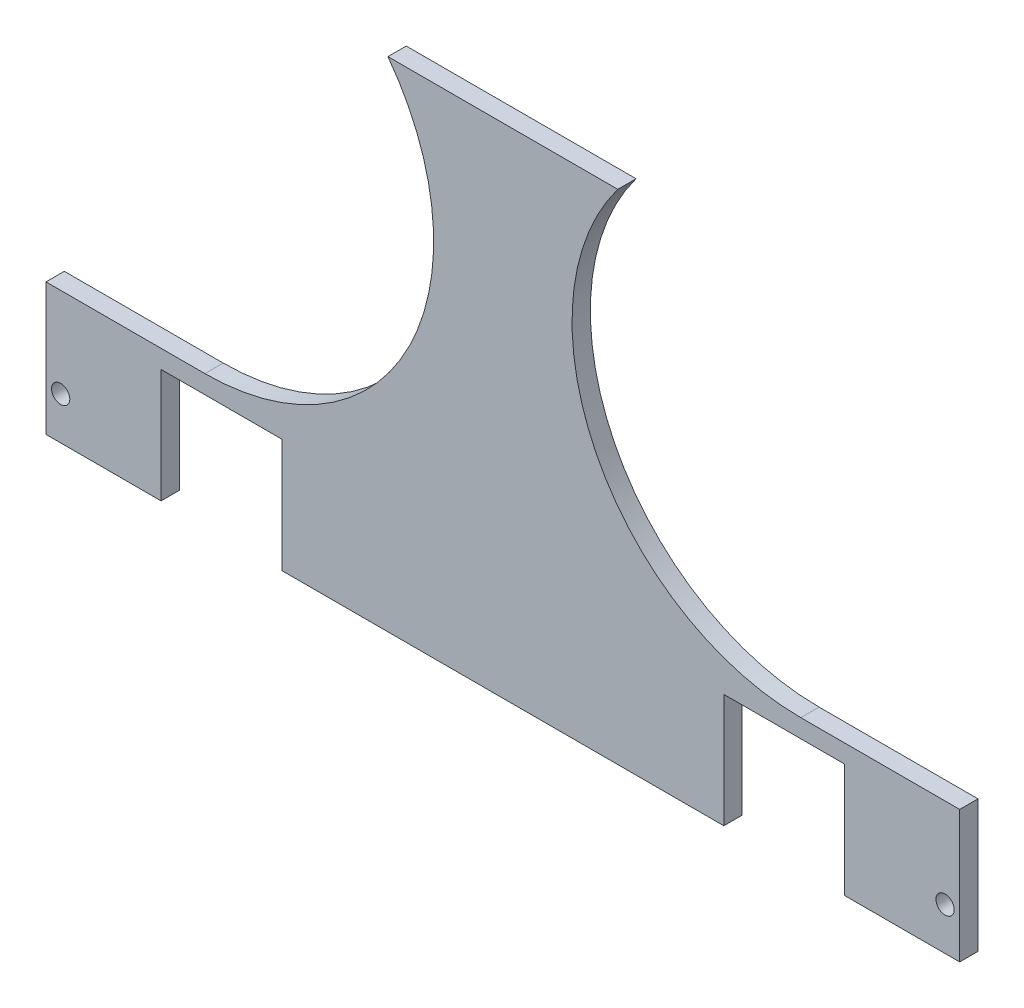
SolidWorks part; units mm, degrees
ref_plane "Front Plane" through (0, 0, 0) normal (0, 0, 1) x (1, 0, 0)
ref_plane "Top Plane" through (0, 0, 0) normal (0, 1, 0) x (1, 0, 0)
ref_plane "Right Plane" through (0, 0, 0) normal (1, 0, 0) x (0, 0, -1)
sketch "Sketch1" plane through (0, 0, 0) normal (0, 0, 1) x (1, 0, 0)
  line L0 (124.8, -69) -> (124.8, -336.4) construction
  line L1 (0, -69) -> (249.6, -69)
  line L2 (0, -69) -> (0, -336.4)
  line L3 (0, -336.4) -> (249.6, -336.4)
  line L4 (249.6, -69) -> (249.6, -336.4)
  line L9 (185.16, -174) -> (218.16, -174)
  line L10 (185.16, -174) -> (185.16, -264)
  line L11 (185.16, -264) -> (218.16, -264)
  line L12 (218.16, -174) -> (218.16, -264)
  line L13 (156.1971, -69) -> (93.4029, -69) construction
  line L14 (31.44, -219) -> (218.16, -219) construction
  line L15 (249.6, -336.4) -> (249.6, -169) construction
  line L21 (0, -169) -> (0, -336.4) construction
  line L25 (249.6, -336.4) -> (0, -336.4) construction
  line L52 (204.16, -174) -> (204.16, -264) construction
  line L53 (194.16, -174) -> (214.16, -174) construction
  line L54 (194.16, -174) -> (194.16, -264) construction
  line L55 (194.16, -264) -> (214.16, -264) construction
  line L56 (214.16, -174) -> (214.16, -264) construction
  line L102 (245.6, -193.5) -> (245.6, -244.5) construction
  line L103 (218.16, -219) -> (245.6, -219) construction
  line L134 (31.44, -219) -> (4, -219) construction
  line L135 (4, -193.5) -> (4, -244.5) construction
  line L139 (35.44, -174) -> (35.44, -264) construction
  line L140 (55.44, -264) -> (35.44, -264) construction
  line L141 (55.44, -174) -> (55.44, -264) construction
  line L142 (55.44, -174) -> (35.44, -174) construction
  line L143 (45.44, -174) -> (45.44, -264) construction
  line L154 (31.44, -174) -> (31.44, -264)
  line L155 (64.44, -264) -> (31.44, -264)
  line L156 (64.44, -174) -> (64.44, -264)
  line L157 (64.44, -174) -> (31.44, -174)
  circle A84 centre (245.6, -193.5) radius 2.5
  circle A85 centre (245.6, -244.5) radius 2.5
  circle A236 centre (4, -244.5) radius 2.5
  circle A237 centre (4, -193.5) radius 2.5
  dimension "D5" = 20
  dimension "D15" = 5
  dimension "D16" = 5
  dimension "D2" = 105
  dimension "D3" = 4
  dimension "D4" = 90
  dimension "D6" = 90
  dimension "D7" = 9
  dimension "D14" = 89.36
  dimension "D17" = 25.5
  dimension "D18" = 4
extrude "Boss-Extrude1" add sketch "Sketch1" along normal blind 5
sketch "Sketch2" plane through (0, 0, 5) normal (0, 0, 1) x (1, 0, 0)
  line L0 (-0.8818, -199.1061) -> (0.8939, -68.1182) construction
  line L1 (377.0835, -204.2298) -> (378.8591, -73.2419) construction
  line L2 (-0.8818, -199.1061) -> (377.0835, -204.2298) construction
  line L3 (14.5032, -15.3834) -> (11.5694, -19.4322) construction
  line L4 (11.5694, -19.4322) -> (65.6935, -58.6513) construction
  line L5 (75.64, -59.684) -> (14.5032, -15.3834) construction
  line L6 (0.8939, -68.1182) -> (378.8591, -73.2419) construction
  line L7 (0.8532, -71.1179) -> (378.8185, -76.2416) construction
  line L8 (-0.8412, -196.1064) -> (377.1241, -201.2301) construction
  line L9 (14.5032, -15.3834) -> (17.4371, -11.3347) construction
  line L10 (17.4371, -11.3347) -> (71.5611, -50.5537) construction
  line L11 (252.1356, -199.5358) -> (253.8299, -74.5473) construction
  line L12 (127.9943, -135.3472) -> (252.9828, -137.0415) construction
  line L13 (127.1471, -197.8414) -> (128.8414, -72.8529) construction
  line L14 (249.6, -69) -> (0, -69) construction
  line L15 (0, -69) -> (0, -336.4) construction
  circle A0 centre (65.5, -134.5) radius 62.5 construction
  circle A1 centre (315.477, -137.8887) radius 62.5 construction
  circle A2 centre (65.5, -134.5) radius 65.5 construction
  circle A3 centre (190.4885, -136.1943) radius 62.5 construction
  circle A4 centre (75.64, -59.684) radius 75.5 construction
  circle A5 centre (75.64, -59.684) radius 2.5 construction
  circle A6 centre (55.3961, -45.015) radius 1.5 construction
  arc A7 (65.6935, -58.6513) -> (71.5611, -50.5537) centre (75.64, -59.684) ccw construction
  dimension "D1" = 125
  dimension "D2" = 125
  dimension "D3" = 5
  dimension "D6" = 3
  dimension "D7" = 10
  dimension "D10" = 125
  dimension "D8" = 3
  dimension "D4" = 5
  dimension "D5" = 25
  dimension "D9" = 5
ref_plane "Plane1"
sketch "Sketch6" plane through (0, 0, 5) normal (0, 0, 1) x (1, 0, 0)
  line L9 (43.4029, -44) -> (0, -44)
  line L10 (206.1971, -169) -> (249.6, -169)
  line L11 (249.6, -169) -> (249.6, -44)
  line L12 (249.6, -44) -> (206.1971, -44)
  line L13 (43.4029, -44) -> (0, -44) construction
  line L18 (43.4029, -169) -> (0, -169)
  line L19 (43.4029, -169) -> (0, -169) construction
  line L23 (0, -44) -> (0, -169)
  line L24 (0, -336.4) -> (249.6, -336.4)
  line L25 (0, -44) -> (0, -169) construction
  line L26 (0, -336.4) -> (0, -205.0954)
  line L27 (249.6, -336.4) -> (249.6, -205.0954)
  line L28 (0, -205.0954) -> (249.6, -205.0954)
  line L29 (249.6, -44) -> (249.6, -169) construction
  line L31 (64.8, -205.0954) -> (59.8, -205.0954) construction
  arc A1 (206.1971, -44) -> (206.1971, -169) centre (206.1971, -106.5) ccw construction
  arc A2 (206.1971, -44) -> (206.1971, -169) centre (206.1971, -106.5) ccw
  arc A3 (43.4029, -169) -> (43.4029, -44) centre (43.4029, -106.5) ccw
  arc A4 (43.4029, -169) -> (43.4029, -44) centre (43.4029, -106.5) ccw construction
extrude "Cut-Extrude4" cut sketch "Sketch6" against normal through all
